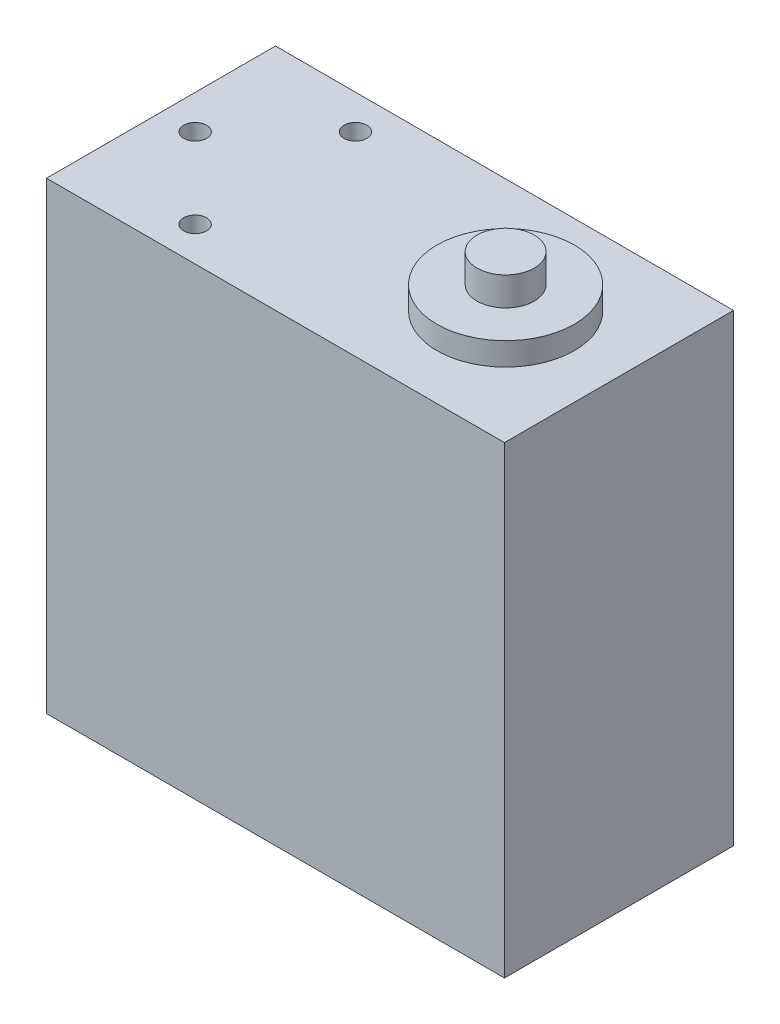
SolidWorks part; units mm, degrees
ref_plane "前视基准面" through (0, 0, 0) normal (0, 0, 1) x (1, 0, 0)
ref_plane "上视基准面" through (0, 0, 0) normal (0, 1, 0) x (1, 0, 0)
ref_plane "右视基准面" through (0, 0, 0) normal (1, 0, 0) x (0, 0, -1)
sketch "草图1" plane through (0, 0, 0) normal (0, 0, 1) x (1, 0, 0)
  line L1 (0, 0) -> (40, 0)
  line L2 (0, 0) -> (0, 40.5)
  line L3 (0, 40.5) -> (40, 40.5)
  line L4 (40, 0) -> (40, 40.5)
  dimension "D1" = 40.5
  dimension "D2" = 40
extrude "凸台-拉伸1" add sketch "草图1" along normal blind 20
sketch "草图2" plane through (0, 40.5, 0) normal (0, 1, 0) x (1, 0, 0)
  line L0 (20, 0) -> (20, -20) construction
  line L1 (40, 0) -> (0, 0) construction
  line L2 (40, -20) -> (0, -20) construction
  line L3 (0, -10) -> (40, -10) construction
  line L4 (0, -20) -> (0, 0) construction
  line L5 (40, -20) -> (40, 0) construction
  circle A0 centre (30.1, -10) radius 6
  point P14 (20, -10)
  dimension "D1" = 10.1
extrude "凸台-拉伸2" add sketch "草图2" along normal blind 2
ref_plane "基准面1" through (0, 20.25, 0) normal (0, 1, 0) x (1, 0, 0)
mirror "镜向1" about plane through (0, 20.25, 0) normal (0, 1, 0) of "凸台-拉伸2"
sketch "草图4" plane through (0, 42.5, 0) normal (0, 1, 0) x (1, 0, 0)
  circle A0 centre (30.1, -10) radius 2.5
extrude "凸台-拉伸3" add sketch "草图4" along normal blind 2.5
sketch "草图5" plane through (0, -2, 0) normal (0, -1, 0) x (1, 0, 0)
  circle A0 centre (30.1, 10) radius 2.5
extrude "凸台-拉伸4" add sketch "草图5" along normal blind 2.5
sketch "草图6" plane through (0, 40.5, 0) normal (0, 1, 0) x (1, 0, 0)
  line L0 (0, -20) -> (0, 0) construction
  line L1 (40, 0) -> (0, 0) construction
  circle A0 centre (9.98, -3) radius 1
  circle A1 centre (9.98, -17) radius 1
  circle A2 centre (2.98, -10) radius 1
  dimension "D1" = 9.98
  dimension "D4" = 7
  dimension "D2" = 3
  dimension "D5" = 7
  dimension "D3" = 2
extrude "切除-拉伸1" cut sketch "草图6" against normal blind 2.5
sketch "草图7" plane through (0, 0, 0) normal (0, -1, 0) x (1, 0, 0)
  line L0 (0, 20) -> (0, 0) construction
  line L1 (0, 20) -> (40, 20) construction
  circle A0 centre (2.5, 17.5) radius 1
  circle A1 centre (17.5, 17.5) radius 1
  circle A2 centre (17.5, 2.5) radius 1
  circle A3 centre (2.5, 2.5) radius 1
  dimension "D1" = 2.5
  dimension "D2" = 2.5
  dimension "D3" = 2
  dimension "D4" = 2
extrude "切除-拉伸2" cut sketch "草图7" against normal blind 2.5
